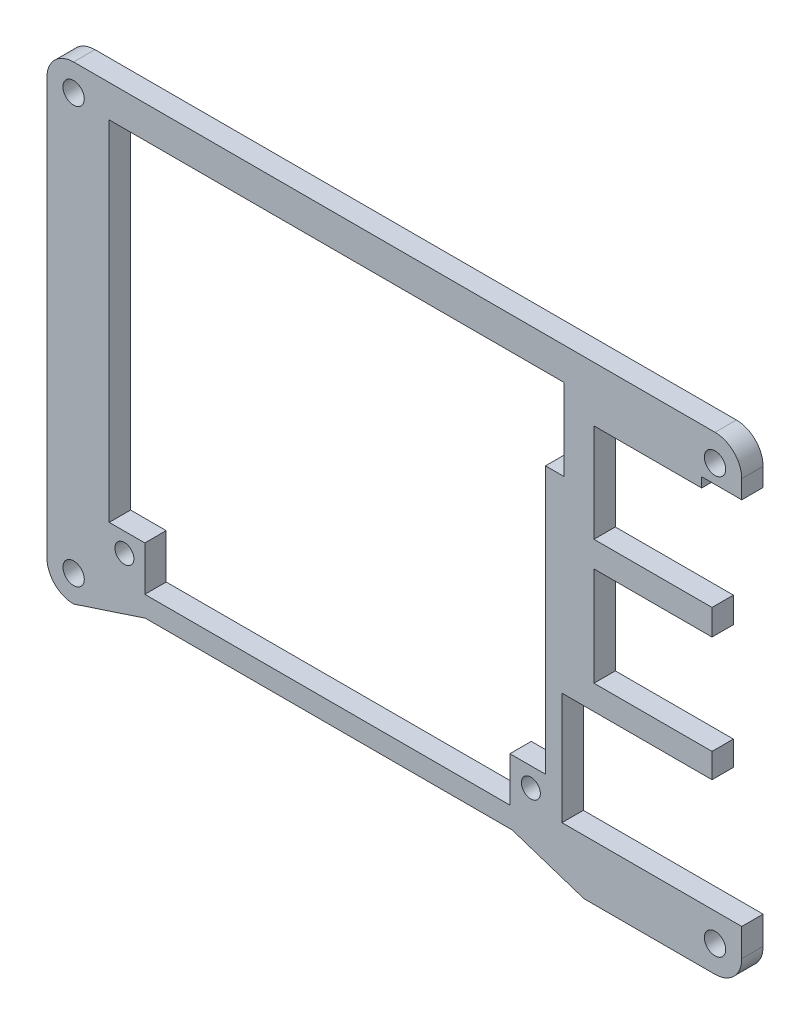
SolidWorks part; units mm, degrees
ref_plane "Front Plane" through (0, 0, 0) normal (0, 0, 1) x (1, 0, 0)
ref_plane "Top Plane" through (0, 0, 0) normal (0, 1, 0) x (1, 0, 0)
ref_plane "Right Plane" through (0, 0, 0) normal (1, 0, 0) x (0, 0, -1)
sketch "Sketch1" plane through (0, 0, 0) normal (0, 0, 1) x (1, 0, 0)
  line L1 (61.2149, 24.0683) -> (61.2149, 26.6839) construction
  line L2 (57.4049, 30.5077) -> (-34.0849, 30.5077) construction
  line L5 (56.975, 4.9979) -> (56.975, 8.6582) construction
  line L9 (56.975, -12.628) -> (56.975, -9.1218) construction
  line L10 (35.575, -12.628) -> (56.975, -12.628) construction
  line L11 (35.575, -28.6278) -> (35.575, -12.628) construction
  line L12 (61.2149, -28.6278) -> (35.575, -28.6278) construction
  line L13 (61.2149, -32.6134) -> (61.2149, -28.6278) construction
  line L14 (38.7143, -36.451) -> (57.405, -36.451) construction
  line L15 (28.4743, -33.0844) -> (38.7143, -36.451) construction
  line L16 (-23.8449, -33.0844) -> (28.4743, -33.0844) construction
  line L17 (-34.0849, -36.451) -> (-23.8449, -33.0844) construction
  line L18 (-37.8949, 26.6977) -> (-37.8949, -32.641) construction
  line L19 (61.2149, 24.0683) -> (40.1348, 24.0683)
  line L20 (61.2149, 24.0683) -> (61.2149, 26.6839)
  line L21 (57.4049, 30.5077) -> (-34.0849, 30.5077)
  line L22 (40.1348, 24.0683) -> (40.1348, 8.6582)
  line L23 (40.1348, 8.6582) -> (56.975, 8.6582)
  line L24 (56.975, 4.9979) -> (56.975, 8.6582)
  line L25 (56.975, 4.9979) -> (40.1348, 4.9979)
  line L26 (40.1348, 4.9979) -> (40.1348, -9.1218)
  line L27 (40.1348, -9.1218) -> (56.975, -9.1218)
  line L28 (56.975, -12.628) -> (56.975, -9.1218)
  line L29 (35.575, -12.628) -> (56.975, -12.628)
  line L30 (35.575, -28.6278) -> (35.575, -12.628)
  line L31 (61.2149, -28.6278) -> (35.575, -28.6278)
  line L32 (61.2149, -32.6134) -> (61.2149, -28.6278)
  line L33 (38.7143, -36.451) -> (57.405, -36.451)
  line L34 (28.4743, -33.0844) -> (38.7143, -36.451)
  line L35 (-23.8449, -33.0844) -> (28.4743, -33.0844)
  line L36 (-34.0849, -36.451) -> (-23.8449, -33.0844)
  line L37 (-37.8949, 26.6977) -> (-37.8949, -32.641)
  line L38 (-23.4169, -23.6989) -> (-23.4169, 9.8012) construction
  line L39 (-29.0049, 25.897) -> (31.6883, 25.897)
  line L40 (-29.0049, 25.897) -> (-29.0049, 18.087)
  line L41 (-29.0049, 18.087) -> (31.6883, 18.087)
  line L42 (31.6883, 25.897) -> (31.6883, 18.087)
  line L43 (-29.0049, 9.8012) -> (-23.4169, 9.8012)
  line L44 (-29.0049, 9.8012) -> (-29.0049, -13.5668)
  line L45 (-29.0049, -13.5668) -> (-23.4169, -13.5668)
  line L46 (-23.4169, 9.8012) -> (-23.4169, -13.5668)
  line L47 (-29.0049, 9.2932) -> (-23.4169, 9.2932)
  line L50 (13.845, -8.3602) -> (19.2484, -8.3602)
  line L51 (13.845, -8.3602) -> (13.845, -30.9668)
  line L52 (13.845, -30.9668) -> (19.2484, -30.9668)
  line L53 (19.2484, -8.3602) -> (19.2484, -30.9668)
  arc A0 (61.2149, 26.6839) -> (57.4049, 30.5077) centre (57.4049, 26.6977) ccw construction
  arc A2 (57.405, -36.451) -> (61.2149, -32.6134) centre (57.405, -32.641) ccw construction
  arc A3 (-37.8949, -32.641) -> (-34.0849, -36.451) centre (-34.0849, -32.641) ccw construction
  arc A4 (-34.0849, 30.5077) -> (-37.8949, 26.6977) centre (-34.0849, 26.6977) ccw construction
  arc A7 (61.2149, 26.6839) -> (57.4049, 30.5077) centre (57.4049, 26.6977) ccw
  circle A8 centre (57.405, -32.641) radius 1.524
  arc A9 (57.405, -36.451) -> (61.2149, -32.6134) centre (57.405, -32.641) ccw
  arc A10 (-37.8949, -32.641) -> (-34.0849, -36.451) centre (-34.0849, -32.641) ccw
  arc A11 (-34.0849, 30.5077) -> (-37.8949, 26.6977) centre (-34.0849, 26.6977) ccw
  circle A12 centre (-34.0849, -32.641) radius 1.524
  circle A13 centre (-34.0849, 26.6977) radius 1.524
  circle A15 centre (57.4049, 26.6977) radius 1.524
  dimension "D5" = 3.048
  dimension "D1" = 23.368
  dimension "D2" = 0.508
  dimension "D3" = 16.8402
  dimension "D4" = 16.8402
extrude "Boss-Extrude1" add sketch "Sketch1" along normal blind 3.048
sketch "Sketch2" plane through (0, 0, 3.048) normal (0, 0, 1) x (1, 0, 0)
  line L2 (-37.8949, 26.6977) -> (-37.8949, -32.641) construction
  line L5 (57.4049, 30.5077) -> (-34.0849, 30.5077) construction
  line L6 (-10.2851, -8.9639) -> (-10.2851, 8.0033) construction
  line L7 (-8.7865, -10.4625) -> (8.1807, -10.4625) construction
  line L8 (9.6793, -8.9639) -> (9.6793, 8.0033) construction
  line L9 (8.1807, 9.5019) -> (-8.7865, 9.5019) construction
  line L10 (-10.2851, -10.4625) -> (9.6793, 9.5019) construction
  circle A0 centre (-0.3029, -0.4803) radius 10.922
  circle A1 centre (-10.2851, -10.4625) radius 1.4986
  circle A2 centre (-10.2851, 9.5019) radius 1.4986
  circle A3 centre (9.6793, -10.4625) radius 1.4986
  circle A4 centre (9.6793, 9.5019) radius 1.4986
  dimension "D1" = 26.67
  dimension "D2" = 20.066
  dimension "D3" = 21.844
  dimension "D4" = 16.9672
  dimension "D5" = 2.9972
extrude "Cut-Extrude1" cut sketch "Sketch2" against normal through all
sketch "Sketch3" plane through (0, 0, 3.048) normal (0, 0, 1) x (1, 0, 0)
  line L0 (13.845, -30.9668) -> (19.2484, -30.9668) construction
  line L1 (-29.0049, 25.897) -> (31.6883, 25.897)
  line L2 (-29.0049, 25.897) -> (-29.0049, -30.9668)
  line L3 (-29.0049, -30.9668) -> (31.6883, -30.9668)
  line L4 (31.6883, 25.897) -> (31.6883, -30.9668)
  line L5 (31.6883, 25.897) -> (31.6883, 18.087) construction
extrude "Boss-Extrude2" add sketch "Sketch3" against normal up to vertex (3.048 mm away) up to point (-29.0049, 25.897, 0)
sketch "Sketch4" [suppressed] plane through (0, 0, 3.048) normal (0, 0, 1) x (1, 0, 0)
  circle A0 centre (-34.0849, -32.641) radius 1.524
  circle A1 centre (57.405, -32.641) radius 1.524
  circle A2 centre (-34.0849, -32.641) radius 1.524
  circle A3 centre (-34.0849, 26.6977) radius 1.524
  circle A4 centre (57.4049, 26.6977) radius 1.524
  dimension "D1" = 3.048
extrude "Cut-Extrude2" [suppressed] cut sketch "Sketch4" against normal through all
sketch "Sketch5" plane through (0, 0, 3.048) normal (0, 0, 1) x (1, 0, 0)
  line L1 (-29.0049, 25.897) -> (35.88, 25.897)
  line L2 (-29.0049, 25.897) -> (-29.0049, 14.277)
  line L3 (-29.0049, 14.277) -> (35.88, 14.277)
  line L4 (35.88, 25.897) -> (35.88, 14.277)
  line L19 (57.4049, 30.5077) -> (-34.0849, 30.5077)
  line L20 (-37.8949, 26.6977) -> (-37.8949, -32.641)
  line L21 (-34.0849, -36.451) -> (-23.8449, -33.0844)
  line L22 (-23.8449, -33.0844) -> (28.4743, -33.0844)
  line L23 (28.4743, -33.0844) -> (38.7143, -36.451)
  line L24 (38.7143, -36.451) -> (57.405, -36.451)
  line L25 (61.2149, -32.6134) -> (61.2149, -28.6278)
  line L26 (61.2149, -28.6278) -> (35.575, -28.6278)
  line L27 (35.575, -28.6278) -> (35.575, -12.628)
  line L28 (35.575, -12.628) -> (56.975, -12.628)
  line L29 (56.975, -12.628) -> (56.975, -9.1218)
  line L30 (56.975, -9.1218) -> (40.1348, -9.1218)
  line L31 (40.1348, -9.1218) -> (40.1348, 4.9979)
  line L32 (40.1348, 4.9979) -> (56.975, 4.9979)
  line L33 (56.975, 4.9979) -> (56.975, 8.6582)
  line L34 (56.975, 8.6582) -> (40.1348, 8.6582)
  line L35 (40.1348, 8.6582) -> (40.1348, 24.0683)
  line L36 (40.1348, 24.0683) -> (61.2149, 24.0683)
  line L37 (61.2149, 24.0683) -> (61.2149, 26.6839)
  line L38 (57.4049, 30.5077) -> (-34.0849, 30.5077)
  line L39 (-37.8949, 26.6977) -> (-37.8949, -32.641)
  line L40 (-34.0849, -36.451) -> (-23.8449, -33.0844)
  line L41 (-23.8449, -33.0844) -> (28.4743, -33.0844)
  line L42 (28.4743, -33.0844) -> (38.7143, -36.451)
  line L43 (38.7143, -36.451) -> (57.405, -36.451)
  line L44 (61.2149, -32.6134) -> (61.2149, -28.6278)
  line L45 (61.2149, -28.6278) -> (35.575, -28.6278)
  line L46 (35.575, -28.6278) -> (35.575, -12.628)
  line L47 (35.575, -12.628) -> (56.975, -12.628)
  line L48 (56.975, -12.628) -> (56.975, -9.1218)
  line L49 (56.975, -9.1218) -> (40.1348, -9.1218)
  line L50 (40.1348, -9.1218) -> (40.1348, 4.9979)
  line L51 (40.1348, 4.9979) -> (56.975, 4.9979)
  line L52 (56.975, 4.9979) -> (56.975, 8.6582)
  line L53 (56.975, 8.6582) -> (40.1348, 8.6582)
  line L54 (40.1348, 8.6582) -> (40.1348, 24.0683)
  line L55 (40.1348, 24.0683) -> (61.2149, 24.0683)
  line L56 (61.2149, 24.0683) -> (61.2149, 26.6839)
  circle A0 centre (-26.8395, -26.5725) radius 2.7305
  circle A1 centre (31.136, -26.5725) radius 2.7305
  arc A4 (-34.0849, 30.5077) -> (-37.8949, 26.6977) centre (-34.0849, 26.6977) ccw
  arc A5 (-37.8949, -32.641) -> (-34.0849, -36.451) centre (-34.0849, -32.641) ccw
  arc A6 (57.405, -36.451) -> (61.2149, -32.6134) centre (57.405, -32.641) ccw
  arc A7 (61.2149, 26.6839) -> (57.4049, 30.5077) centre (57.4049, 26.6977) ccw
  arc A8 (-34.0849, 30.5077) -> (-37.8949, 26.6977) centre (-34.0849, 26.6977) ccw
  arc A9 (-37.8949, -32.641) -> (-34.0849, -36.451) centre (-34.0849, -32.641) ccw
  arc A10 (57.405, -36.451) -> (61.2149, -32.6134) centre (57.405, -32.641) ccw
  arc A11 (61.2149, 26.6839) -> (57.4049, 30.5077) centre (57.4049, 26.6977) ccw
  dimension "D1" = 0
extrude "Cut-Extrude3" cut sketch "Sketch5" against normal through all contours L4 L1 L2 L3 | A0 | A1
sketch "Sketch6" plane through (0, 0, 3.048) normal (0, 0, 1) x (1, 0, 0)
  circle A0 centre (-26.8395, -26.5725) radius 1.3525
  circle A1 centre (31.136, -26.5725) radius 1.3525
  circle A2 centre (-26.8395, -26.5725) radius 2.7305
  circle A3 centre (31.136, -26.5725) radius 2.7305
  dimension "D1" = 2.7051
  dimension "D2" = 5.461
extrude "Boss-Extrude3" add sketch "Sketch6" against normal blind 3.048
sketch "Sketch7" plane through (0, 0, 3.048) normal (0, 0, 1) x (1, 0, 0)
  line L1 (55.4999, 22.6713) -> (40.1348, 22.6713)
  line L2 (55.4999, 22.6713) -> (55.4999, 24.0683)
  line L3 (55.4999, 24.0683) -> (40.1348, 24.0683)
  line L4 (40.1348, 22.6713) -> (40.1348, 24.0683)
  dimension "D1" = 1.397
  dimension "D2" = 15.3651
extrude "Boss-Extrude4" add sketch "Sketch7" against normal blind 3.048
sketch "Sketch8" plane through (0, 0, 3.048) normal (0, 0, 1) x (1, 0, 0)
  line L0 (-23.9249, -23.823) -> (-23.9249, -30.173)
  line L1 (-29.0049, 14.277) -> (33.2251, 14.277)
  line L2 (-29.0049, 14.277) -> (-29.0049, -23.823)
  line L3 (-29.0049, -23.823) -> (33.2251, -23.823)
  line L4 (33.2251, 14.277) -> (33.2251, -23.823)
  line L5 (-23.9249, -30.173) -> (28.1451, -30.173)
  line L6 (28.1451, -30.173) -> (28.1451, -23.823)
  line M32 (35.88, 14.277) -> (-29.0049, 14.277)
  dimension "D1" = 38.1
  dimension "D2" = 6.35
  dimension "D3" = 5.08
  dimension "D4" = 5.08
  dimension "D5" = 62.23
extrude "Cut-Extrude4" cut sketch "Sketch8" against normal through all contours L4 L2 L3 M32 | L5 L6 L3 L0
